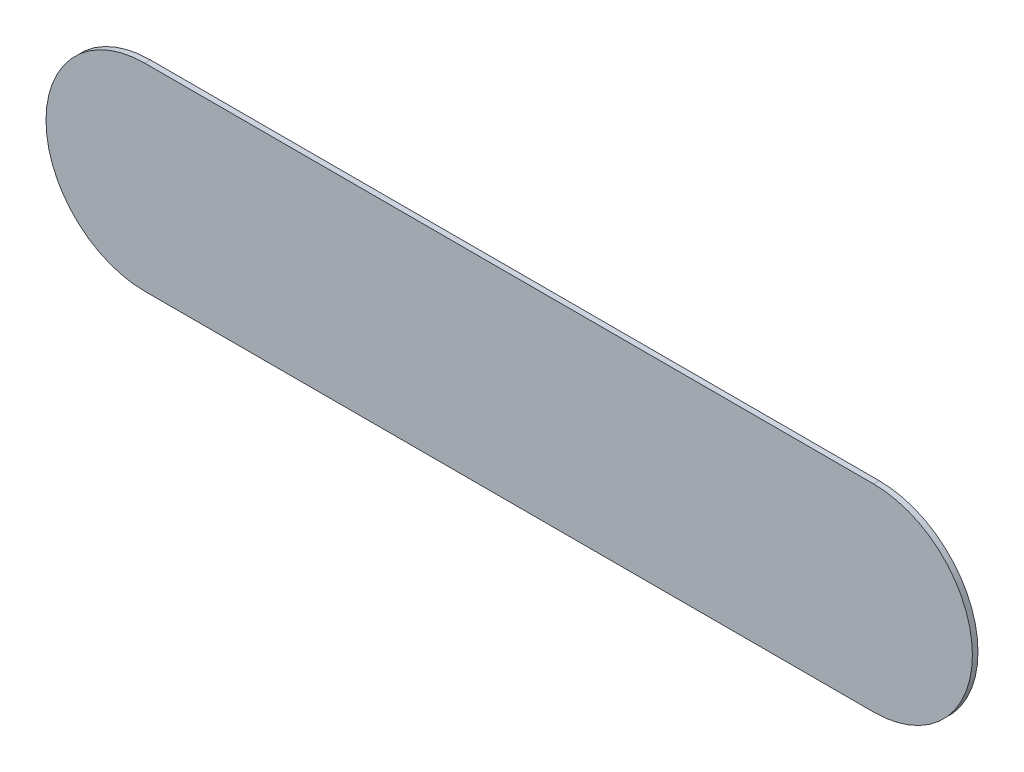
SolidWorks part; units mm, degrees
ref_plane "Front Plane" through (0, 0, 0) normal (0, 0, 1) x (1, 0, 0)
ref_plane "Top Plane" through (0, 0, 0) normal (0, 1, 0) x (1, 0, 0)
ref_plane "Right Plane" through (0, 0, 0) normal (1, 0, 0) x (0, 0, -1)
sketch "Sketch1" plane through (0, 0, 0) normal (0, 0, 1) x (1, 0, 0)
  line L0 (0, 0) -> (65, 0) construction
  line L1 (0, 8.81) -> (65, 8.81)
  line L2 (0, -8.81) -> (65, -8.81)
  arc A0 (0, 8.81) -> (0, -8.81) centre (0, 0) ccw
  arc A1 (65, -8.81) -> (65, 8.81) centre (65, 0) ccw
  point P3 (32.5, 0)
  dimension "D2" = 8.81
  dimension "D1" = 65
extrude "Boss-Extrude1" add sketch "Sketch1" along normal blind 0.5
